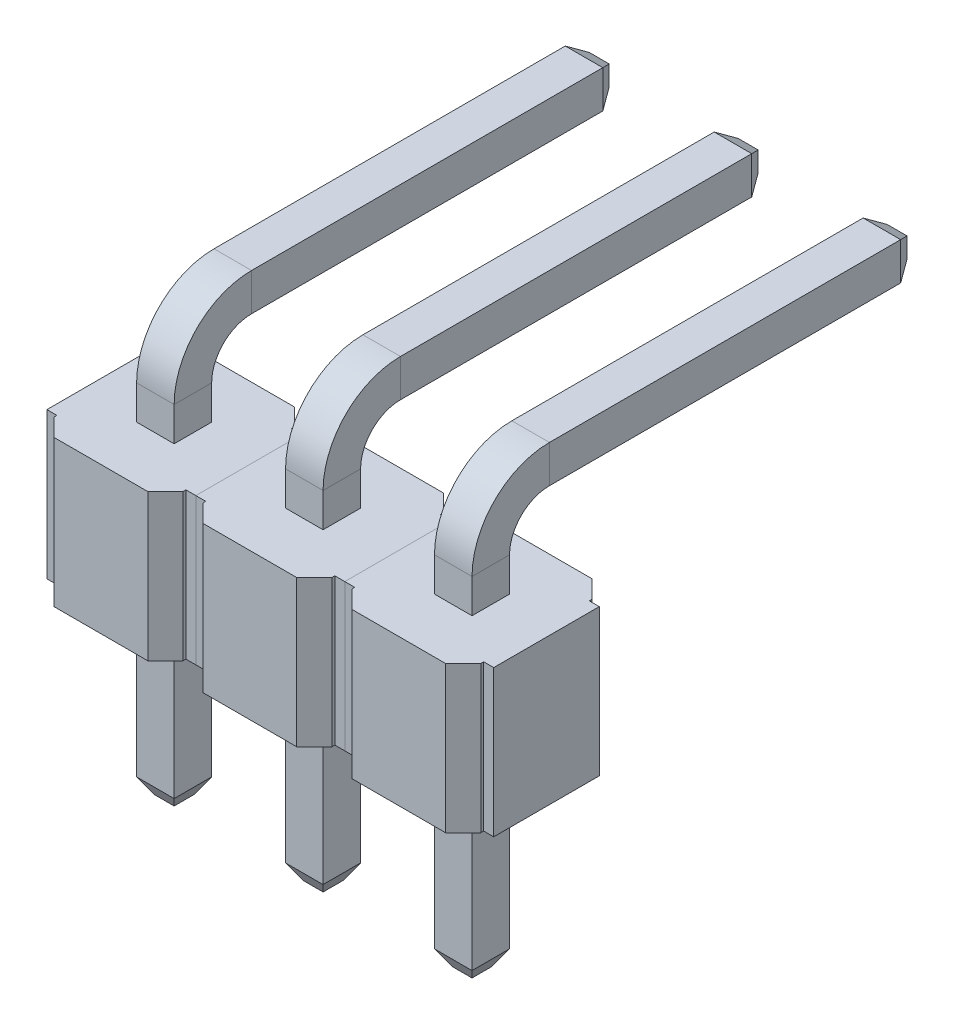
SolidWorks part; units mm, degrees
ref_plane "Front" through (0, 0, 0) normal (0, 0, 1) x (1, 0, 0)
ref_plane "Top" through (0, 0, 0) normal (0, 1, 0) x (1, 0, 0)
ref_plane "Right" through (0, 0, 0) normal (1, 0, 0) x (0, 0, -1)
sketch "Эскиз2" plane through (0, 0, 0) normal (1, 0, 0) x (0, 0, -1)
  line L0 (0, 0) -> (0, -3)
  line L1 (0, 0) -> (0, 3.08)
  line L2 (1, 4.08) -> (7.25, 4.08)
  arc A0 (1, 4.08) -> (0, 3.08) centre (1, 3.08) ccw
  point P7 (0, 4.08)
  dimension "D4" = 1
  dimension "D1" = 3
  dimension "D2" = 4.08
  dimension "D3" = 7.25
sketch "Эскиз3" plane through (0, 0, 0) normal (0, 1, 0) x (1, 0, 0)
  line L1 (-0.32, -0.32) -> (0.32, -0.32)
  line L2 (-0.32, -0.32) -> (-0.32, 0.32)
  line L3 (-0.32, 0.32) -> (0.32, 0.32)
  line L4 (0.32, -0.32) -> (0.32, 0.32)
  line L5 (-0.32, -0.32) -> (0.32, 0.32) construction
  line L6 (-0.32, 0.32) -> (0.32, -0.32) construction
  point P0 (0, 0)
sweep "PIN PROFILE" add profiles "Эскиз3" path "Эскиз2"
chamfer "END PIN PROFILE" distance 0.15 angle 60 8 edges at (0, -3, -0.32) (-0.32, -3, 0) (0, -3, 0.32) (0.32, -3, 0) (0, 4.4, -7.25) (-0.32, 4.08, -7.25) (0, 3.76, -7.25) (0.32, 4.08, -7.25)
sketch "Эскиз4" plane through (0, 0, 0) normal (0, 1, 0) x (1, 0, 0)
  line L0 (-1.1, 0.9) -> (-1.1, 1.25)
  line L1 (-1.1, -1.25) -> (1.1, -1.25)
  line L2 (-1.1, -1.25) -> (-1.1, -0.9)
  line L3 (-1.1, 1.25) -> (1.1, 1.25)
  line L4 (1.1, -1.25) -> (1.1, -0.9)
  line L5 (-1.1, -1.25) -> (1.1, 1.25) construction
  line L6 (-1.1, 1.25) -> (1.1, -1.25) construction
  line L7 (-1.27, -0.9) -> (-1.1, -0.9)
  line L8 (-1.27, -0.9) -> (-1.27, 0.9)
  line L9 (-1.27, 0.9) -> (-1.1, 0.9)
  line L10 (1.27, -0.9) -> (1.27, 0.9)
  line L11 (-1.27, -0.9) -> (1.27, 0.9) construction
  line L12 (-1.27, 0.9) -> (1.27, -0.9) construction
  line L13 (1.1, 0.9) -> (1.1, 1.25)
  line L14 (1.1, -0.9) -> (1.27, -0.9)
  line L15 (1.1, 0.9) -> (1.27, 0.9)
  point P0 (0, 0)
  point P5 (0, 0)
  dimension "D1" = 2.2
  dimension "D2" = 2.5
  dimension "D3" = 1.8
  dimension "D4" = 2.54
extrude "BASE BODY" add sketch "Эскиз4" along normal blind 2.5 separate body
chamfer "BB CHAMFER" distance 0.3 angle 45 4 edges at (-1.1, 1.25, -1.25) (1.1, 1.25, -1.25) (-1.1, 1.25, 1.25) (1.1, 1.25, 1.25)
pattern_linear "LP ALL" count 2 spacing 2.54 along (-1, 0, 0) count 2 spacing 2.54 along (1, 0, 0) of bodies 102 101
equation "\"D2@Эскиз2\"=4.4-0.64/2"
equation "\"D3@Эскиз2\"=6+2.5/2"
